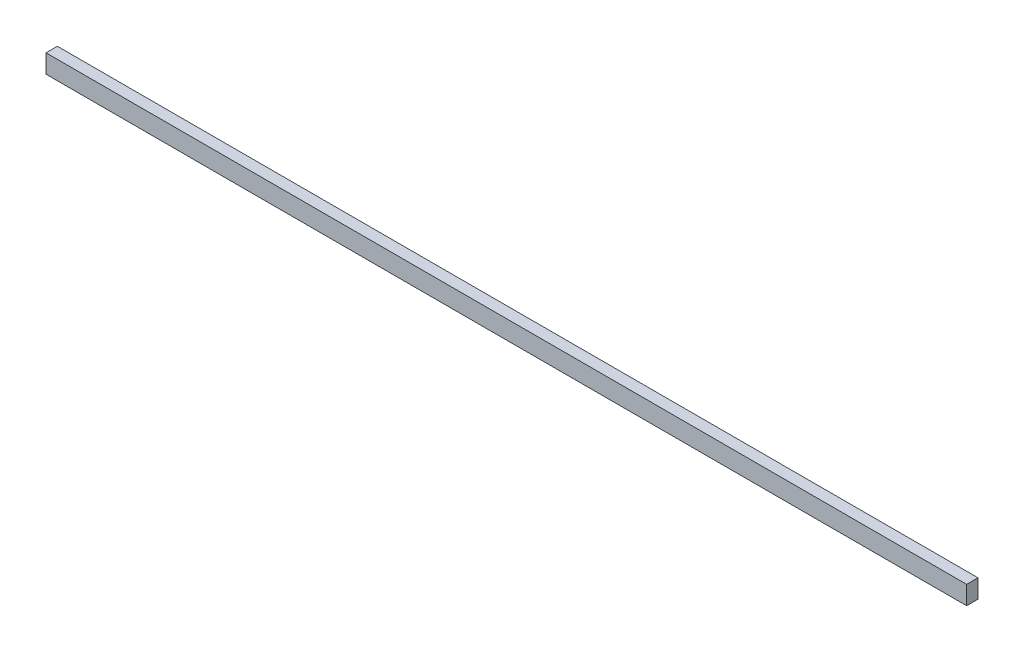
SolidWorks part; units mm, degrees
ref_plane "Front Plane" through (0, 0, 0) normal (0, 0, 1) x (1, 0, 0)
ref_plane "Top Plane" through (0, 0, 0) normal (0, 1, 0) x (1, 0, 0)
ref_plane "Right Plane" through (0, 0, 0) normal (1, 0, 0) x (0, 0, -1)
sketch "Sketch1" plane through (0, 0, 0) normal (0, 0, 1) x (1, 0, 0)
  line L1 (0, 0) -> (472.77, 0)
  line L2 (0, 0) -> (0, 9.525)
  line L3 (0, 9.525) -> (472.77, 9.525)
  line L4 (472.77, 0) -> (472.77, 9.525)
  dimension "D1" = 472.77
  dimension "D2" = 9.525
extrude "Boss-Extrude1" add sketch "Sketch1" along normal blind 5.83
